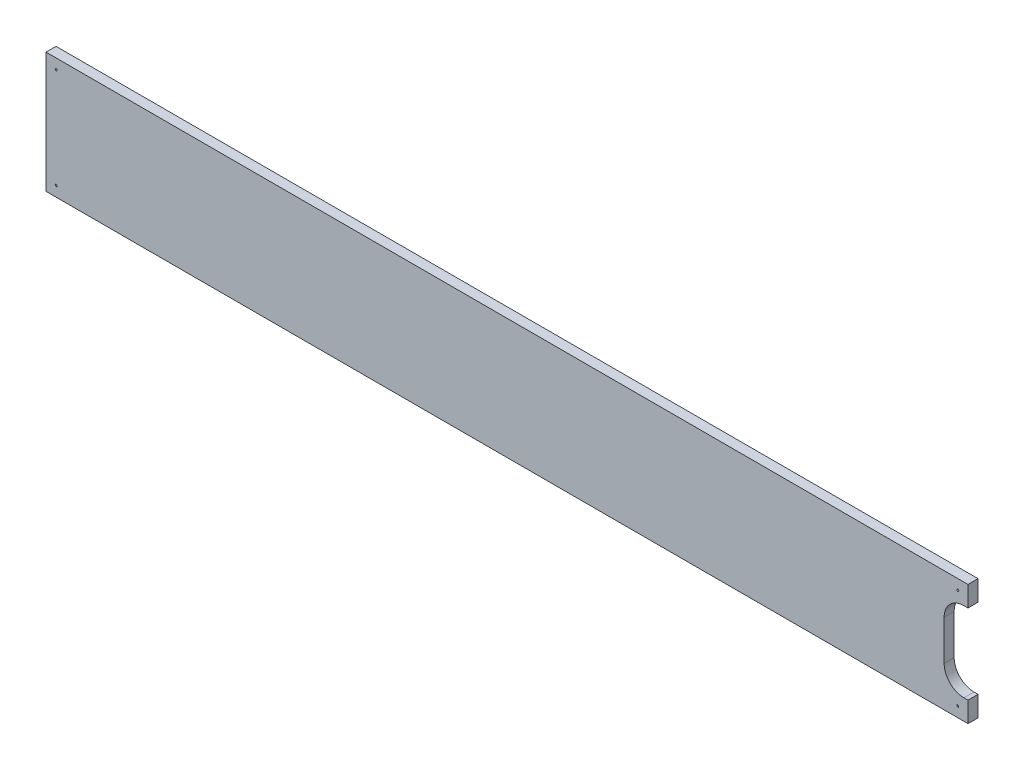
SolidWorks part; units mm, degrees
material "Contreplaqué pin"
ref_plane "Plan de face" through (0, 0, 0) normal (0, 0, 1) x (1, 0, 0)
ref_plane "Plan de dessus" through (0, 0, 0) normal (0, 1, 0) x (1, 0, 0)
ref_plane "Plan de droite" through (0, 0, 0) normal (1, 0, 0) x (0, 0, -1)
sketch "Esquisse1" plane through (0, 0, 0) normal (0, 0, 1) x (1, 0, 0)
  line L0 (-0.1, -0.1) -> (460.1, -0.1)
  line L1 (0, 0) -> (460, 0) construction
  line L2 (0, 0) -> (0, 60) construction
  line L3 (0, 60) -> (460, 60) construction
  line L4 (460, 0) -> (460, 60) construction
  line L5 (460.1, -0.1) -> (460.1, 60.1)
  line L6 (-0.1, 60.1) -> (460.1, 60.1)
  line L7 (-0.1, -0.1) -> (-0.1, 60.1)
  dimension "D1" = 460
  dimension "D2" = 60
  dimension "D3" = 0.1
extrude "Boss.-Extru.1" add sketch "Esquisse1" along normal blind 5
hole_wizard "Diamètre du perçage Ø1.0 (1)1" positions "Esquisse2" profile "Esquisse3" hole size "Ø1.0" standard "DIN" end condition through all
sketch "Esquisse2" plane through (0, 0, 5) normal (0, 0, 1) x (1, 0, 0)
  line L4 (-0.1, 60.1) -> (-0.1, -0.1) construction
  line L5 (460.1, 60.1) -> (-0.1, 60.1) construction
  line L6 (460.1, -0.1) -> (460.1, 60.1) construction
  line L8 (-0.1, -0.1) -> (460.1, -0.1) construction
  point P0 (5, 55)
  point P2 (5, 5)
  point P4 (455, 5)
  point P6 (455, 55)
  point P23 (-0.1, 58.833)
  point P28 (1.2297, 60.1)
  point P33 (460.1, 16.2707)
  point P38 (448.2968, -0.1)
  point P43 (451.6213, -0.1)
  point P48 (451.9596, -0.1)
  dimension "D1" = 5.1
  dimension "D2" = 5.1
  dimension "D3" = 5.1
  dimension "D4" = 5.1
sketch "Esquisse3" plane through (5, 55, 5) normal (1, 0, 0) x (0, -1, 0)
  line L0 (0, 0) -> (0, 5)
  line L1 (0, 5) -> (0.5, 5)
  line L2 (0.5, 5) -> (0.5, 0)
  line L5 (0.5, 0) -> (0, 0)
  line L11 (0, -6.35) -> (0, 107.95) construction
  dimension "Diamètre du perçage jusqu'au prochain" = 1
  dimension "Profondeur du perçage jusqu'au prochain" = 5
sketch "Esquisse4" plane through (0, 0, 5) normal (0, 0, 1) x (1, 0, 0)
  line L1 (460.1, 50) -> (458.1, 50) construction
  line L2 (460.1, 50) -> (460.1, 10)
  line L3 (460.1, 10) -> (458.1, 10) construction
  line L4 (448.1, 40) -> (448.1, 20) construction
  line L8 (460.1, 60.1) -> (-0.1, 60.1) construction
  line L9 (460.1, -0.1) -> (460.1, 60.1) construction
  line L10 (-0.1, -0.1) -> (460.1, -0.1) construction
  line L11 (460.1, 49.9) -> (458.1, 49.9)
  line L12 (448.2, 40) -> (448.2, 20)
  line L13 (460.1, 10.1) -> (458.1, 10.1)
  line L14 (460, 49.9) -> (460, 10.1) construction
  line L15 (460, 49.9) -> (458.1, 49.9) construction
  line L16 (460, 10.1) -> (458.1, 10.1) construction
  arc A0 (458.1, 10) -> (448.1, 20) centre (458.1, 20) cw construction
  arc A1 (448.1, 40) -> (458.1, 50) centre (458.1, 40) cw construction
  arc A2 (448.2, 40) -> (458.1, 49.9) centre (458.1, 40) cw
  arc A3 (458.1, 10.1) -> (448.2, 20) centre (458.1, 20) cw
  point P6 (0, 0)
  point P12 (448.1, 10)
  point P16 (459.9992, -0.1)
  point P17 (459.6553, 60.1)
  dimension "D4" = 10
  dimension "D1" = 12
  dimension "D2" = 10.1
  dimension "D3" = 10.1
  dimension "D5" = 0.1
extrude "Enlèv. mat.-Extru.1" cut sketch "Esquisse4" against normal up to next contours A3 L13 L2 L11 A2 L12
